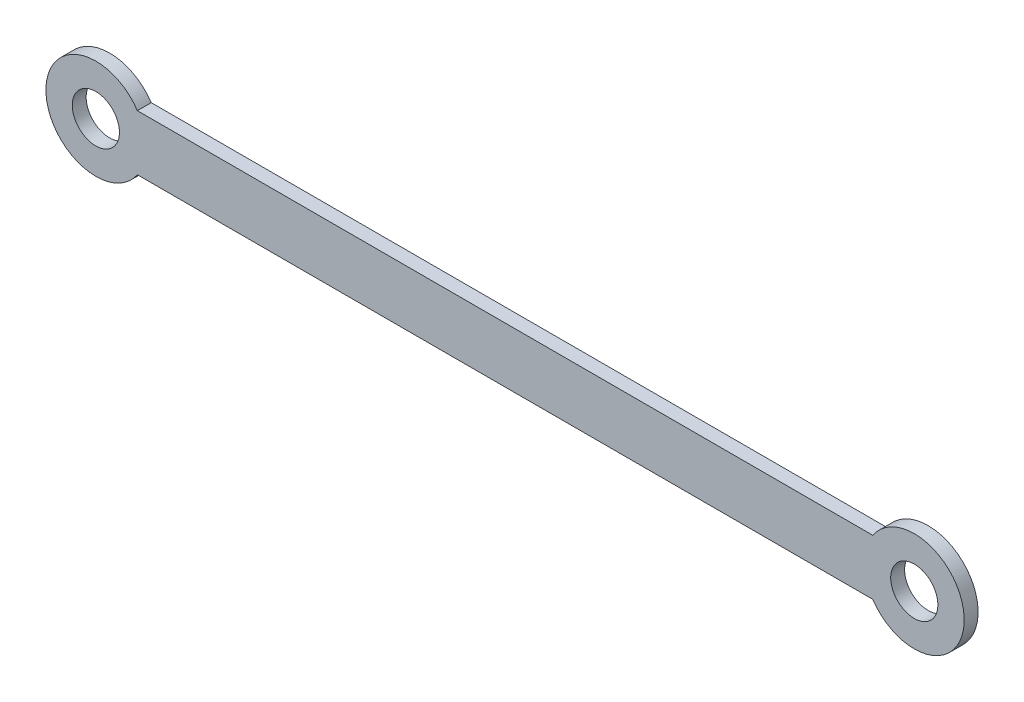
SolidWorks part; units mm, degrees
ref_plane "前视基准面" through (0, 0, 0) normal (0, 0, 1) x (1, 0, 0)
ref_plane "上视基准面" through (0, 0, 0) normal (0, 1, 0) x (1, 0, 0)
ref_plane "右视基准面" through (0, 0, 0) normal (1, 0, 0) x (0, 0, -1)
sketch "草图1" plane through (0, 0, 0) normal (0, 0, 1) x (1, 0, 0)
  line L0 (0, 0) -> (147.5, 0) construction
  line L1 (7.4833, 5) -> (140.0167, 5)
  line L2 (7.4833, -5) -> (140.0167, -5)
  arc A0 (7.4833, 5) -> (7.4833, -5) centre (0, 0) ccw
  arc A1 (140.0167, -5) -> (140.0167, 5) centre (147.5, 0) ccw
  circle A2 centre (0, 0) radius 4.25
  circle A3 centre (147.5, 0) radius 4.25
  dimension "D2" = 8.5
  dimension "D3" = 8.5
  dimension "D4" = 18
  dimension "D5" = 18
  dimension "D1" = 147.5
  dimension "D6" = 5
extrude "凸台-拉伸1" add sketch "草图1" along normal blind 2.5
